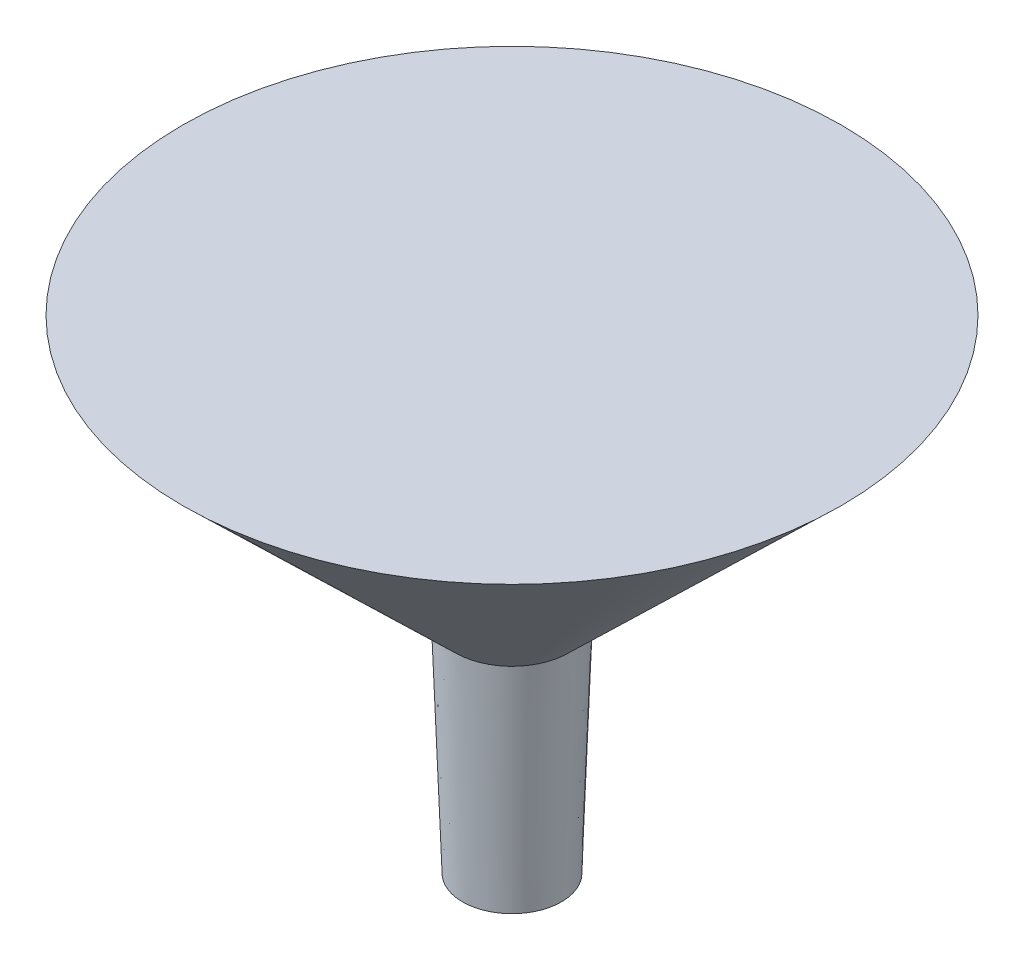
SolidWorks part; units mm, degrees
ref_plane "Front Plane" through (0, 0, 0) normal (0, 0, 1) x (1, 0, 0)
ref_plane "Top Plane" through (0, 0, 0) normal (0, 1, 0) x (1, 0, 0)
ref_plane "Right Plane" through (0, 0, 0) normal (1, 0, 0) x (0, 0, -1)
sketch "Sketch1" plane through (0, 0, 0) normal (1, 0, 0) x (0, 0, -1)
  line L0 (0, 13.97) -> (0, -13.97)
  line L1 (0, -13.97) -> (2.8585, -13.97)
  line L2 (2.8585, -13.97) -> (3.302, -1.27)
  line L3 (3.302, -1.27) -> (19.05, 13.97)
  line L4 (19.05, 13.97) -> (0, 13.97)
  line L5 (3.175, -4.9068) -> (0, -4.9068) construction
  point P3 (3.175, -6.2261)
  point P9 (0, 0)
  dimension "D1" = 2
  dimension "D2" = 12.7
  dimension "D3" = 27.94
  dimension "D4" = 19.05
  dimension "D5" = 3.175
  dimension "D6" = 3.302
revolve "Revolve1" add sketch "Sketch1" angle 360 about L0
